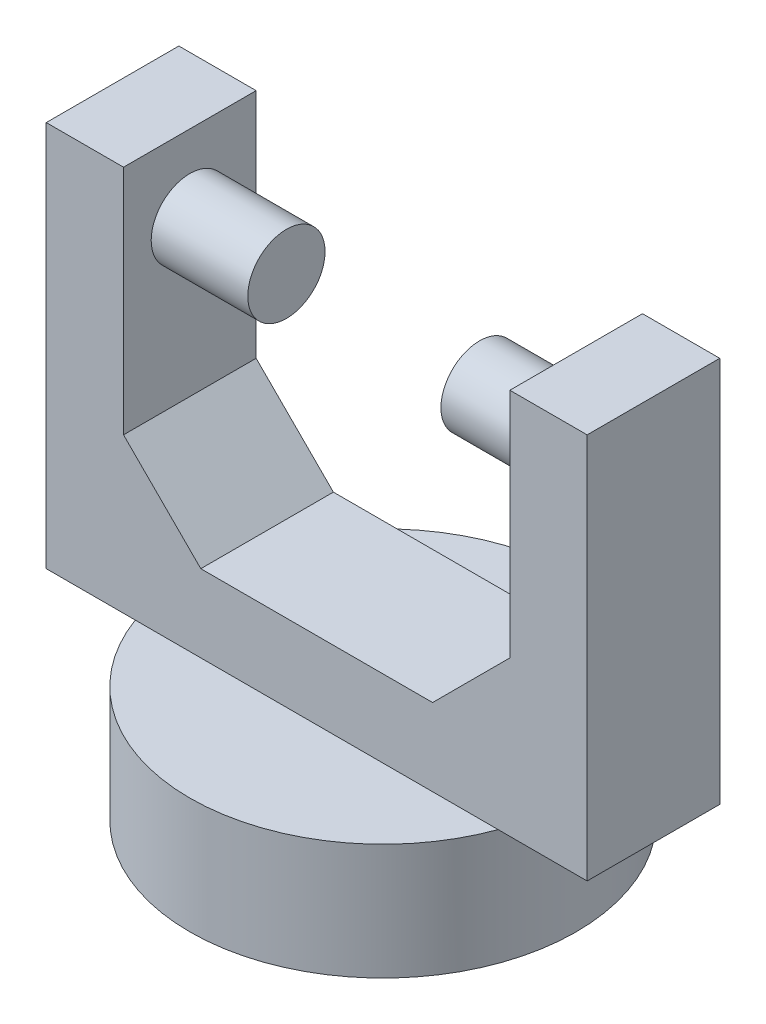
SolidWorks part; units mm, degrees
ref_plane "Front Plane" through (0, 0, 0) normal (0, 0, 1) x (1, 0, 0)
ref_plane "Top Plane" through (0, 0, 0) normal (0, 1, 0) x (1, 0, 0)
ref_plane "Right Plane" through (0, 0, 0) normal (1, 0, 0) x (0, 0, -1)
sketch "Sketch1" plane through (0, 0, 0) normal (0, 1, 0) x (1, 0, 0)
  circle A0 centre (0, 0) radius 12.5
  dimension "D1" = 25
extrude "Boss-Extrude1" add sketch "Sketch1" along normal blind 7.5
sketch "Sketch2" plane through (0, 7.5, 0) normal (0, 1, 0) x (1, 0, 0)
  line L1 (-17.5, 4.2904) -> (17.5, 4.2904)
  line L2 (-17.5, 4.2904) -> (-17.5, -4.2904)
  line L3 (-17.5, -4.2904) -> (17.5, -4.2904)
  line L4 (17.5, 4.2904) -> (17.5, -4.2904)
  point P4 (17.5, 0)
  point P6 (0, 4.2904)
  dimension "D1" = 35
  dimension "D3" = 8.5808
extrude "Boss-Extrude2" add sketch "Sketch2" along normal blind 25
sketch "Sketch3" plane through (0, 32.5, 0) normal (0, 1, 0) x (1, 0, 0)
  line L0 (17.5, 4.2904) -> (-17.5, 4.2904) construction
  line L1 (-12.5, 4.2904) -> (12.5, 4.2904)
  line L2 (-12.5, 4.2904) -> (-12.5, -4.2904)
  line L3 (-12.5, -4.2904) -> (12.5, -4.2904)
  line L4 (12.5, 4.2904) -> (12.5, -4.2904)
  line L5 (-17.5, -4.2904) -> (17.5, -4.2904) construction
  line L6 (17.5, -4.2904) -> (17.5, 4.2904) construction
  line L7 (-17.5, 4.2904) -> (-17.5, -4.2904) construction
  dimension "D1" = 5
  dimension "D2" = 5
extrude "Cut-Extrude1" cut sketch "Sketch3" against normal blind 20
sketch "Sketch4" plane through (-12.5, 0, 0) normal (1, 0, 0) x (0, 0, -1)
  line L0 (4.2904, 12.5) -> (-4.2904, 12.5) construction
  line L1 (4.2904, 32.5) -> (-4.2904, 32.5) construction
  circle A0 centre (0, 27.5) radius 2.5
  point P8 (0, 32.5)
  dimension "D1" = 5
  dimension "D2" = 15
extrude "Boss-Extrude3" add sketch "Sketch4" along normal blind 6.25
sketch "Sketch5" plane through (12.5, 0, 0) normal (-1, 0, 0) x (0, 0, 1)
  circle A0 centre (0, 27.5) radius 2.5
  circle A1 centre (0, 27.5) radius 2.5 construction
  dimension "D1" = 5
extrude "Boss-Extrude4" add sketch "Sketch5" along normal blind 6.25
chamfer "Chamfer1" distance 5 angle 45 1 edges at (-12.5, 12.5, 0)
chamfer "Chamfer2" distance 5 angle 45 1 edges at (12.5, 12.5, 0)
